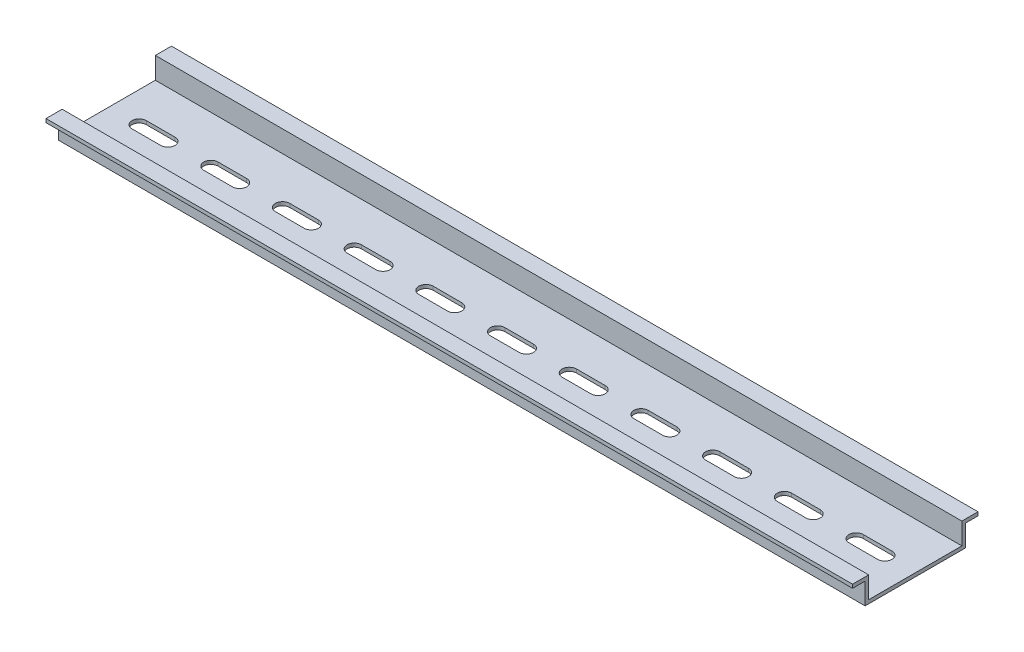
SolidWorks part; units mm, degrees
ref_plane "Front Plane" through (0, 0, 0) normal (0, 0, 1) x (1, 0, 0)
ref_plane "Top Plane" through (0, 0, 0) normal (0, 1, 0) x (1, 0, 0)
ref_plane "Right Plane" through (0, 0, 0) normal (1, 0, 0) x (0, 0, -1)
sketch "Sketch1" plane through (0, 0, 0) normal (0, 1, 0) x (1, 0, 0)
  line L1 (112.5, -17.5) -> (-112.5, -17.5)
  line L2 (112.5, -17.5) -> (112.5, 17.5)
  line L3 (112.5, 17.5) -> (-112.5, 17.5)
  line L4 (-112.5, -17.5) -> (-112.5, 17.5)
  line L5 (112.5, -17.5) -> (-112.5, 17.5) construction
  line L6 (112.5, 17.5) -> (-112.5, -17.5) construction
  point P0 (0, 0)
  dimension "D1" = 225
  dimension "D2" = 35
extrude "Boss-Extrude1" add sketch "Sketch1" along normal mid plane 7
sketch "Sketch2" plane through (112.5, 0, 0) normal (1, 0, 0) x (0, 0, -1)
  line L0 (-13, -2.5) -> (0, -2.5)
  line L1 (-17.5, 3.5) -> (17.5, 3.5) construction
  line L3 (17.5, 3.5) -> (17.5, -3.5) construction
  line L5 (13, 3.5) -> (13, -2.5)
  line L6 (17.5, 2.5) -> (14, 2.5)
  line L7 (14, 2.5) -> (14, -3.5)
  line L8 (-17.5, -3.5) -> (17.5, -3.5) construction
  line L9 (0, -3.5) -> (0, 3.5) construction
  line L11 (13, -2.5) -> (0, -2.5)
  line L13 (-14, 2.5) -> (-14, -3.5)
  line L14 (-17.5, 2.5) -> (-14, 2.5)
  line L15 (-13, 3.5) -> (-13, -2.5)
  line L18 (-13, 3.5) -> (13, 3.5)
  line L19 (-17.5, 2.5) -> (-17.5, -3.5)
  line L20 (17.5, 3.5) -> (13, 3.5) construction
  line L21 (-17.5, -3.5) -> (-14, -3.5)
  line L22 (14, -3.5) -> (17.5, -3.5)
  line L23 (17.5, -3.5) -> (17.5, 2.5)
  line L25 (14, -3.5) -> (0, -3.5) construction
  dimension "D1" = 1
extrude "Cut-Extrude1" cut sketch "Sketch2" against normal through all
sketch "Sketch3" plane through (0, -2.5, 0) normal (0, 1, 0) x (1, 0, 0)
  line L0 (0, 0) -> (6, 0) construction
  line L1 (0, 0) -> (-6, 0) construction
  line L2 (-4, 2) -> (4, 2)
  line L3 (-4, -2) -> (4, -2)
  line L4 (16, 2) -> (24, 2)
  line L5 (16, -2) -> (24, -2)
  line L6 (20, 0) -> (26, 0) construction
  line L7 (20, 0) -> (14, 0) construction
  line L8 (36, 2) -> (44, 2)
  line L9 (36, -2) -> (44, -2)
  line L10 (40, 0) -> (46, 0) construction
  line L11 (40, 0) -> (34, 0) construction
  line L12 (56, 2) -> (64, 2)
  line L13 (56, -2) -> (64, -2)
  line L14 (60, 0) -> (66, 0) construction
  line L15 (60, 0) -> (54, 0) construction
  line L16 (76, 2) -> (84, 2)
  line L17 (76, -2) -> (84, -2)
  line L18 (80, 0) -> (86, 0) construction
  line L19 (80, 0) -> (74, 0) construction
  line L20 (-24, 2) -> (-16, 2)
  line L21 (-24, -2) -> (-16, -2)
  line L22 (-20, 0) -> (-14, 0) construction
  line L23 (-20, 0) -> (-26, 0) construction
  line L24 (-44, 2) -> (-36, 2)
  line L25 (-44, -2) -> (-36, -2)
  line L26 (-40, 0) -> (-34, 0) construction
  line L27 (-40, 0) -> (-46, 0) construction
  line L28 (-64, 2) -> (-56, 2)
  line L29 (-64, -2) -> (-56, -2)
  line L30 (-60, 0) -> (-54, 0) construction
  line L31 (-60, 0) -> (-66, 0) construction
  line L32 (-84, 2) -> (-76, 2)
  line L33 (-84, -2) -> (-76, -2)
  line L34 (-80, 0) -> (-74, 0) construction
  line L35 (-80, 0) -> (-86, 0) construction
  line L36 (-104, 2) -> (-96, 2)
  line L37 (-104, -2) -> (-96, -2)
  line L38 (-100, 0) -> (-94, 0) construction
  line L39 (-100, 0) -> (-106, 0) construction
  line L40 (-124, 2) -> (-116, 2)
  line L41 (-124, -2) -> (-116, -2)
  line L42 (-120, 0) -> (-114, 0) construction
  line L43 (-120, 0) -> (-126, 0) construction
  line L44 (-144, 2) -> (-136, 2)
  line L45 (-144, -2) -> (-136, -2)
  line L46 (-140, 0) -> (-134, 0) construction
  line L47 (-140, 0) -> (-146, 0) construction
  line L48 (96, 2) -> (104, 2)
  line L49 (96, -2) -> (104, -2)
  line L50 (100, 0) -> (106, 0) construction
  line L51 (100, 0) -> (94, 0) construction
  line L52 (116, 2) -> (124, 2)
  line L53 (116, -2) -> (124, -2)
  line L54 (120, 0) -> (126, 0) construction
  line L55 (120, 0) -> (114, 0) construction
  line L56 (136, 2) -> (144, 2)
  line L57 (136, -2) -> (144, -2)
  line L58 (140, 0) -> (146, 0) construction
  line L59 (140, 0) -> (134, 0) construction
  arc A1 (4, -2) -> (4, 2) centre (4, 0) ccw
  arc A3 (-4, 2) -> (-4, -2) centre (-4, 0) ccw
  arc A4 (24, -2) -> (24, 2) centre (24, 0) ccw
  arc A5 (16, 2) -> (16, -2) centre (16, 0) ccw
  arc A6 (44, -2) -> (44, 2) centre (44, 0) ccw
  arc A7 (36, 2) -> (36, -2) centre (36, 0) ccw
  arc A8 (64, -2) -> (64, 2) centre (64, 0) ccw
  arc A9 (56, 2) -> (56, -2) centre (56, 0) ccw
  arc A10 (84, -2) -> (84, 2) centre (84, 0) ccw
  arc A11 (76, 2) -> (76, -2) centre (76, 0) ccw
  arc A12 (-16, -2) -> (-16, 2) centre (-16, 0) ccw
  arc A13 (-24, 2) -> (-24, -2) centre (-24, 0) ccw
  arc A14 (-36, -2) -> (-36, 2) centre (-36, 0) ccw
  arc A15 (-44, 2) -> (-44, -2) centre (-44, 0) ccw
  arc A16 (-56, -2) -> (-56, 2) centre (-56, 0) ccw
  arc A17 (-64, 2) -> (-64, -2) centre (-64, 0) ccw
  arc A18 (-76, -2) -> (-76, 2) centre (-76, 0) ccw
  arc A19 (-84, 2) -> (-84, -2) centre (-84, 0) ccw
  arc A20 (-96, -2) -> (-96, 2) centre (-96, 0) ccw
  arc A21 (-104, 2) -> (-104, -2) centre (-104, 0) ccw
  arc A22 (-116, -2) -> (-116, 2) centre (-116, 0) ccw
  arc A23 (-124, 2) -> (-124, -2) centre (-124, 0) ccw
  arc A24 (-136, -2) -> (-136, 2) centre (-136, 0) ccw
  arc A25 (-144, 2) -> (-144, -2) centre (-144, 0) ccw
  arc A26 (104, -2) -> (104, 2) centre (104, 0) ccw
  arc A27 (96, 2) -> (96, -2) centre (96, 0) ccw
  arc A28 (124, -2) -> (124, 2) centre (124, 0) ccw
  arc A29 (116, 2) -> (116, -2) centre (116, 0) ccw
  arc A30 (144, -2) -> (144, 2) centre (144, 0) ccw
  arc A31 (136, 2) -> (136, -2) centre (136, 0) ccw
  dimension "D1" = 8
  dimension "D2" = 8
extrude "Cut-Extrude2" cut sketch "Sketch3" against normal through all
